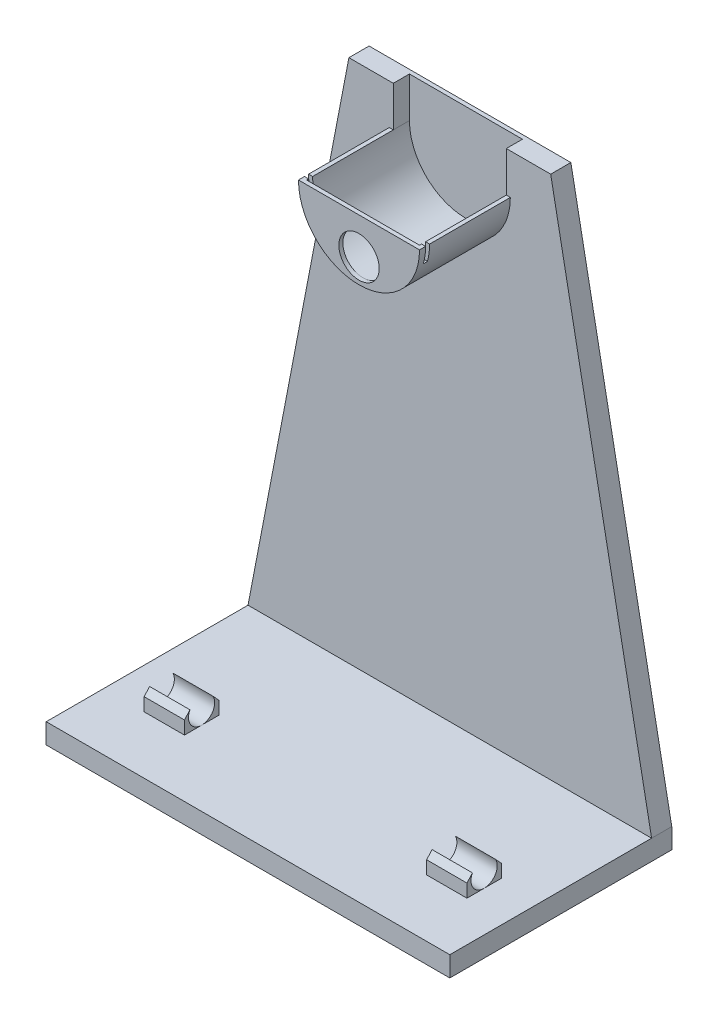
SolidWorks part; units mm, degrees
ref_plane "Front Plane" through (0, 0, 0) normal (0, 0, 1) x (1, 0, 0)
ref_plane "Top Plane" through (0, 0, 0) normal (0, 1, 0) x (1, 0, 0)
ref_plane "Right Plane" through (0, 0, 0) normal (1, 0, 0) x (0, 0, -1)
sketch "Sketch1" plane through (0, 0, 0) normal (0, 0, 1) x (1, 0, 0)
  line L0 (-50, 0) -> (50, 0) construction
  line L1 (0, 0) -> (0, 130) construction
  line L2 (25, 130) -> (-25, 130)
  line L5 (-50, 0) -> (-50, -5)
  line L6 (-50, -5) -> (50, -5)
  line L7 (50, 0) -> (50, -5)
  line L8 (0, 130) -> (0, 100) construction
  line L9 (-25, 130) -> (-50, 0)
  line L10 (25, 130) -> (50, 0)
  point P3 (0, 0)
  point P10 (0, 130)
extrude "Boss-Extrude1" add sketch "Sketch1" along normal blind 5
sketch "Sketch3" plane through (0, 0, 5) normal (0, 0, 1) x (1, 0, 0)
  line L0 (0, 120) -> (0, 110) construction
  line L2 (0, 110) -> (0, 0) construction
  line L3 (0, 110) -> (0, 120) construction
  line L4 (-15, 120) -> (15, 120)
  arc A0 (-15, 120) -> (15, 120) centre (0, 120) ccw
extrude "Boss-Extrude3" add sketch "Sketch3" along normal blind 22.5 contours A0 L4
sketch "Sketch12" plane through (0, 0, 5) normal (0, 0, 1) x (1, 0, 0)
  line L0 (-15, 120) -> (15, 120) construction
  line L1 (-15, 120) -> (15, 120) construction
  line L2 (-15, 120) -> (15, 120) construction
  line L4 (-14, 120) -> (-14, 130)
  line L5 (25, 130) -> (-25, 130) construction
  line L6 (-14, 130) -> (14, 130)
  line L7 (14, 130) -> (14, 120)
  arc A0 (-14, 120) -> (14, 120) centre (0, 120) ccw
  arc A1 (-15, 120) -> (15, 120) centre (0, 120) ccw construction
  point P3 (0, 106)
  point P13 (0, 105)
  dimension "D1" = 14
  dimension "D2" = 1
  dimension "D3" = 1
extrude "Cut-Extrude3" cut sketch "Sketch12" against normal blind 4 and the other way blind 21.5
sketch "Sketch2" plane through (0, 0, 5) normal (0, 0, 1) x (1, 0, 0)
  line L0 (-50, -5) -> (50, -5)
  line L1 (50, -5) -> (50, 0)
  line L2 (50, 0) -> (-50, 0)
  line L3 (-50, 0) -> (-50, -5)
extrude "Boss-Extrude2" add sketch "Sketch2" along normal blind 50
shell "Shell4" [suppressed] thickness 1
sketch "Sketch4" plane through (0, 0, 27.5) normal (0, 0, 1) x (1, 0, 0)
  line L0 (0, 105) -> (0, 111) construction
  arc A0 (-15, 120) -> (15, 120) centre (0, 120) ccw construction
  circle A1 centre (0, 111) radius 5
  dimension "D1" = 10
  dimension "D2" = 6
extrude "Cut-Extrude1" cut sketch "Sketch4" against normal blind 8.5
sketch "Sketch5" plane through (0, 120, 0) normal (0, 1, 0) x (1, 0, 0)
  line L3 (21.4474, -25) -> (21.4474, -26)
  line L4 (21.4474, -26) -> (-20.1929, -26)
  line L6 (-20.1929, -26) -> (-20.1929, -25)
  line L7 (-20.1929, -25) -> (21.4474, -25)
extrude "Cut-Extrude2" cut sketch "Sketch5" against normal blind 4
ref_plane "Plane2" through (35, 0, 0) normal (1, 0, 0) x (0, 0, -1)
ref_plane "Plane3" through (-35, 0, 0) normal (1, 0, 0) x (0, 0, -1)
sketch "Sketch8" plane through (-35, 0, 0) normal (1, 0, 0) x (0, 0, -1)
  line L0 (-27.5, 112.5) -> (-36.5, 112.5) construction
  line L1 (-27.5, 120) -> (-27.5, 105) construction
  line L2 (-36.5, 112.5) -> (-36.5, 3.25) construction
  line L4 (-55, 0) -> (-5, 0) construction
  line L7 (-39.75, 4.3474) -> (-39.75, 4.75) construction
  line L8 (-39.75, 4.75) -> (-33.25, 4.75) construction
  line L9 (-33.25, 4.75) -> (-33.25, 4.3474) construction
  line L13 (-40.75, 3.25) -> (-40.75, 0)
  line L15 (-32.25, 3.25) -> (-32.25, 0)
  line L16 (-33.6169, 4.75) -> (-32.25, 3.25)
  line L17 (-39.3831, 4.75) -> (-40.75, 3.25)
  line L18 (-5, 0) -> (-32.25, 0)
  line L23 (0, -5) -> (0, 0)
  line L24 (0, 0) -> (-5, 0)
  line L25 (-5, 0) -> (-55, 0)
  line L26 (-55, 0) -> (-55, -5)
  line L27 (-55, -5) -> (0, -5)
  line L28 (0, -5) -> (0, 0)
  line L29 (0, 0) -> (-5, 0)
  line L30 (-40.75, 0) -> (-55, 0)
  line L31 (-55, 0) -> (-55, -5)
  line L32 (-55, -5) -> (0, -5)
  arc A1 (-39.3831, 4.75) -> (-33.6169, 4.75) centre (-36.5, 3.25) ccw
  dimension "D1" = 0
sketch "Sketch11" plane through (35, 0, 0) normal (1, 0, 0) x (0, 0, -1)
  line L0 (-27.5, 112.5) -> (-36.5, 112.5) construction
  line L2 (-36.5, 112.5) -> (-36.5, 3.25) construction
  line L7 (-39.75, 4.3474) -> (-39.75, 4.75) construction
  line L8 (-39.75, 4.75) -> (-33.25, 4.75) construction
  line L9 (-33.25, 4.75) -> (-33.25, 4.3474) construction
  line L13 (-40.75, 3.25) -> (-40.75, 0)
  line L15 (-32.25, 3.25) -> (-32.25, 0)
  line L16 (-33.6169, 4.75) -> (-32.25, 3.25)
  line L17 (-39.3831, 4.75) -> (-40.75, 3.25)
  line L18 (-5, 0) -> (-32.25, 0)
  line L28 (0, -5) -> (0, 0)
  line L29 (0, 0) -> (-5, 0)
  line L30 (-40.75, 0) -> (-55, 0)
  line L31 (-55, 0) -> (-55, -5)
  line L32 (-55, -5) -> (0, -5)
  arc A1 (-39.3831, 4.75) -> (-33.6169, 4.75) centre (-36.5, 3.25) ccw
extrude "Boss-Extrude5" add sketch "Sketch8" along normal blind 5 and the other way blind 5
extrude "Boss-Extrude6" add sketch "Sketch11" along normal blind 5 and the other way blind 5
